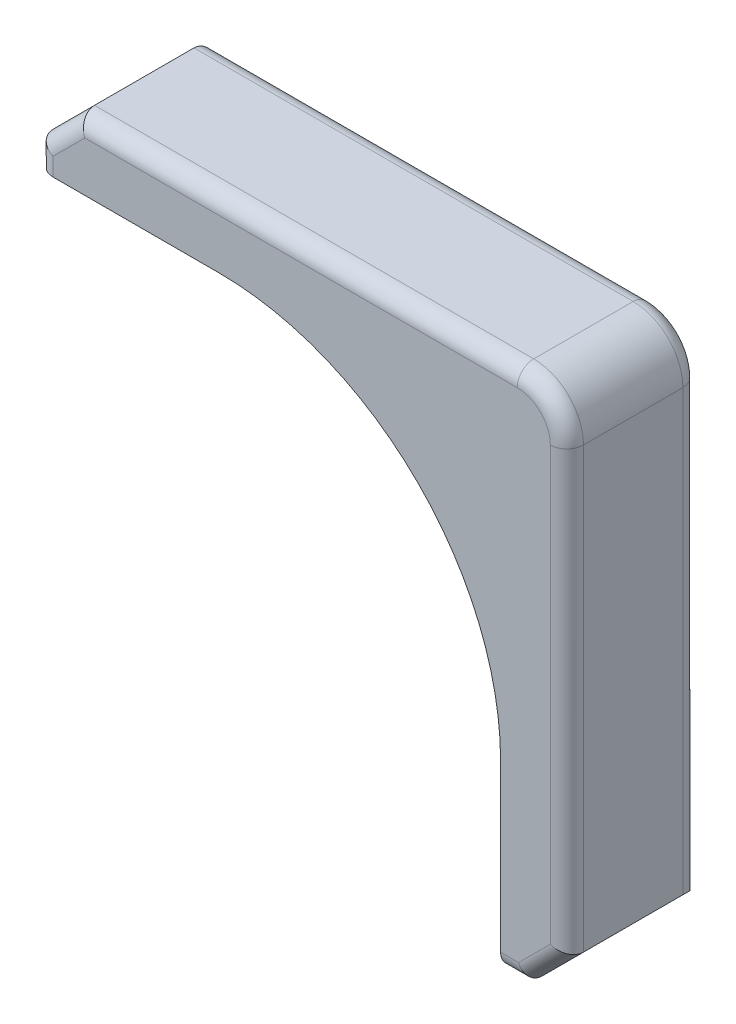
SolidWorks part; units mm, degrees
ref_plane "Спереди" through (0, 0, 0) normal (0, 0, 1) x (1, 0, 0)
ref_plane "Сверху" through (0, 0, 0) normal (0, 1, 0) x (1, 0, 0)
ref_plane "Справа" through (0, 0, 0) normal (1, 0, 0) x (0, 0, -1)
sketch "Эскиз1" plane through (0, 0, 0) normal (0, 0, 1) x (1, 0, 0)
  line L0 (-8.5, 21) -> (18, 21)
  line L1 (17, 0) -> (17, -11)
  line L2 (17, -11) -> (18.5, -11)
  line L3 (18.5, -11) -> (21, -8.5)
  line L4 (21, -8.5) -> (21, 18)
  line L5 (-8.5, 21) -> (-11, 18.5)
  line L6 (-11, 18.5) -> (-11, 17)
  line L7 (-11, 17) -> (0, 17)
  arc A0 (17, 0) -> (0, 17) centre (0, 0) ccw
  arc A1 (21, 18) -> (18, 21) centre (18, 18) ccw
  dimension "D1" = 3
  dimension "D2" = 17
  dimension "D3" = 4
  dimension "D4" = 45
  dimension "D5" = 2.5
  dimension "D6" = 32
extrude "Бобышка-Вытянуть1" add sketch "Эскиз1" along normal blind 8
fillet "Скругление1" radius 1 12 edges at (-11, 17.75, 0) (-9.75, 19.75, 0) (4.75, 21, 0) (20.1213, 20.1213, 0) (21, 4.75, 0) (17.75, -11, 8) (19.75, -9.75, 8) (21, 4.75, 8) (20.1213, 20.1213, 8) (4.75, 21, 8) (-9.75, 19.75, 8) (-11, 17.75, 8)
